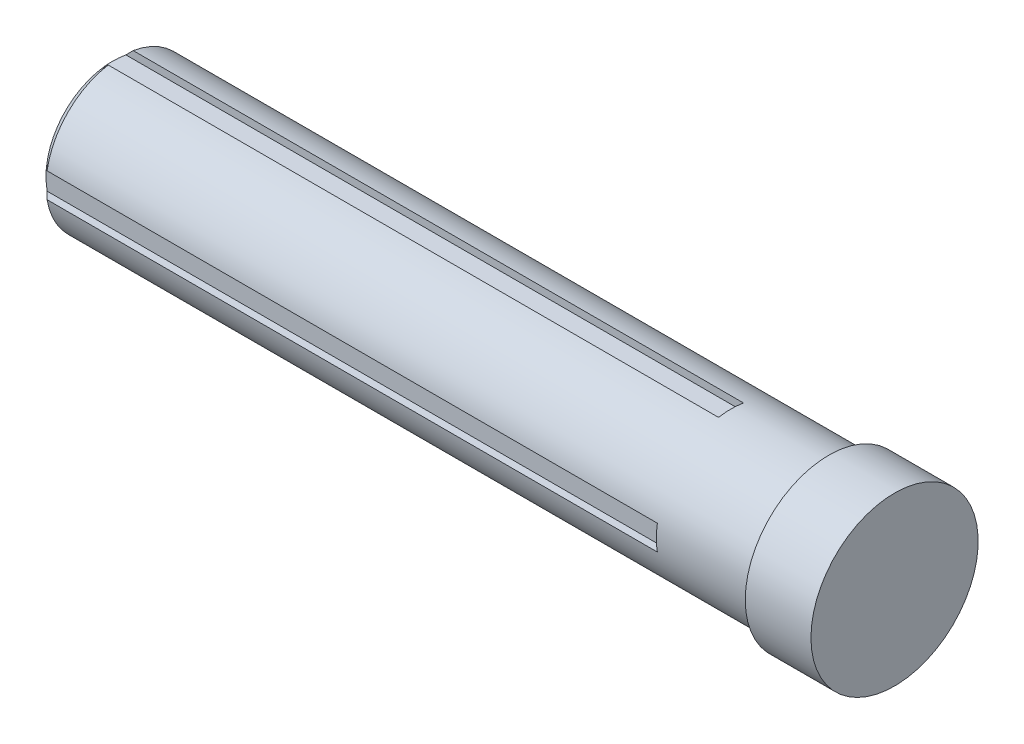
SolidWorks part; units mm, degrees
ref_plane "Front Plane" through (0, 0, 0) normal (0, 0, 1) x (1, 0, 0)
ref_plane "Top Plane" through (0, 0, 0) normal (0, 1, 0) x (1, 0, 0)
ref_plane "Right Plane" through (0, 0, 0) normal (1, 0, 0) x (0, 0, -1)
sketch "Sketch1" plane through (0, 0, 0) normal (0, 0, 1) x (1, 0, 0)
  line L0 (-815.6105, 0) -> (815.6105, 0) construction
  line L1 (-670.5602, 0) -> (-670.5602, 110.8579)
  line L2 (-656.418, 125) -> (529.4398, 125)
  line L3 (529.4398, 125) -> (529.4398, 140)
  line L4 (529.4398, 140) -> (639.4398, 140)
  line L5 (639.4398, 140) -> (639.4398, 0)
  line L6 (-656.418, 125) -> (-670.5602, 110.8579)
  line L7 (-670.5602, 0) -> (639.4398, 0)
  point P4 (0, 0)
  dimension "D2" = 1200
  dimension "D3" = 110
  dimension "D4" = 140
  dimension "D5" = 45
  dimension "D6" = 20
revolve "Revolve1" add sketch "Sketch1" angle 360 about L0
sketch "Sketch2" plane through (-670.5602, 0, 0) normal (-1, 0, 0) x (0, 0, 1)
  line L0 (0, 183.498) -> (0, -183.498) construction
  line L1 (-20.915, 110.8579) -> (20.915, 110.8579)
  line L2 (-20.915, 110.8579) -> (-20.915, 123.2378)
  line L3 (20.915, 110.8579) -> (20.915, 123.2378)
  circle A1 centre (0, 0) radius 125 construction
  circle A3 centre (0, 0) radius 125
  arc A4 (20.915, 123.2378) -> (-20.915, 123.2378) centre (0, 0) ccw
  point P4 (0, 0)
  point P8 (0, 110.8579)
  dimension "D1" = 41.83
  dimension "D2" = 0
extrude "Cut-Extrude1" cut sketch "Sketch2" against normal blind 1036.14 contours A4 L2 L1 L3
pattern_circular "CirPattern1" count 4 over 360 about axis through (0, 0, 0) along (1, 0, 0) of "Cut-Extrude1"
